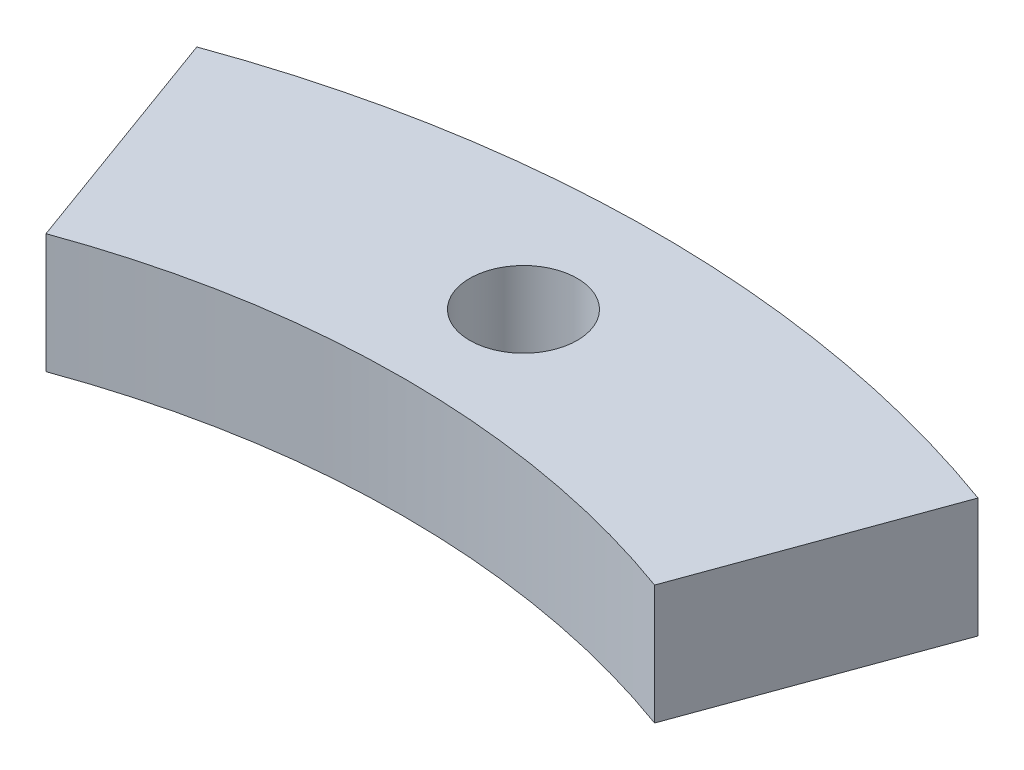
SolidWorks part; units mm, degrees
ref_plane "Front Plane" through (0, 0, 0) normal (0, 0, 1) x (1, 0, 0)
ref_plane "Top Plane" through (0, 0, 0) normal (0, 1, 0) x (1, 0, 0)
ref_plane "Right Plane" through (0, 0, 0) normal (1, 0, 0) x (0, 0, -1)
sketch "Sketch1" plane through (0, 0, 0) normal (0, 1, 0) x (1, 0, 0)
  circle A0 centre (0, 0) radius 38 construction
  circle A1 centre (0, 0) radius 43
  circle A2 centre (0, 0) radius 33.5
  dimension "D1" = 76
  dimension "D2" = 86
  dimension "D3" = 67
extrude "Boss-Extrude1" add sketch "Sketch1" along normal blind 4.5
sketch "Sketch2" plane through (0, 4.5, 0) normal (0, 1, 0) x (1, 0, 0)
  line L0 (0, 0) -> (0, -52.3198)
  line L1 (0, 0) -> (17.8944, 49.1646)
  arc A0 (17.8944, 49.1646) -> (0, -52.3198) centre (0, 0) cw
  dimension "D1" = 160
extrude "Cut-Extrude1" cut sketch "Sketch2" against normal through all both and the other way through all
mirror "Mirror1" about plane through (0, 0, 0) normal (1, 0, 0) of "Cut-Extrude1"
sketch "Sketch3" plane through (0, 4.5, 0) normal (0, 1, 0) x (1, 0, 0)
  line L0 (0, 0) -> (0, 43) construction
  arc A0 (14.7069, 40.4068) -> (-14.7069, 40.4068) centre (0, 0) ccw construction
  circle A1 centre (0, 38) radius 2.025
  dimension "D1" = 4.05
  dimension "D2" = 38
extrude "Cut-Extrude2" cut sketch "Sketch3" against normal through all both and the other way through all
